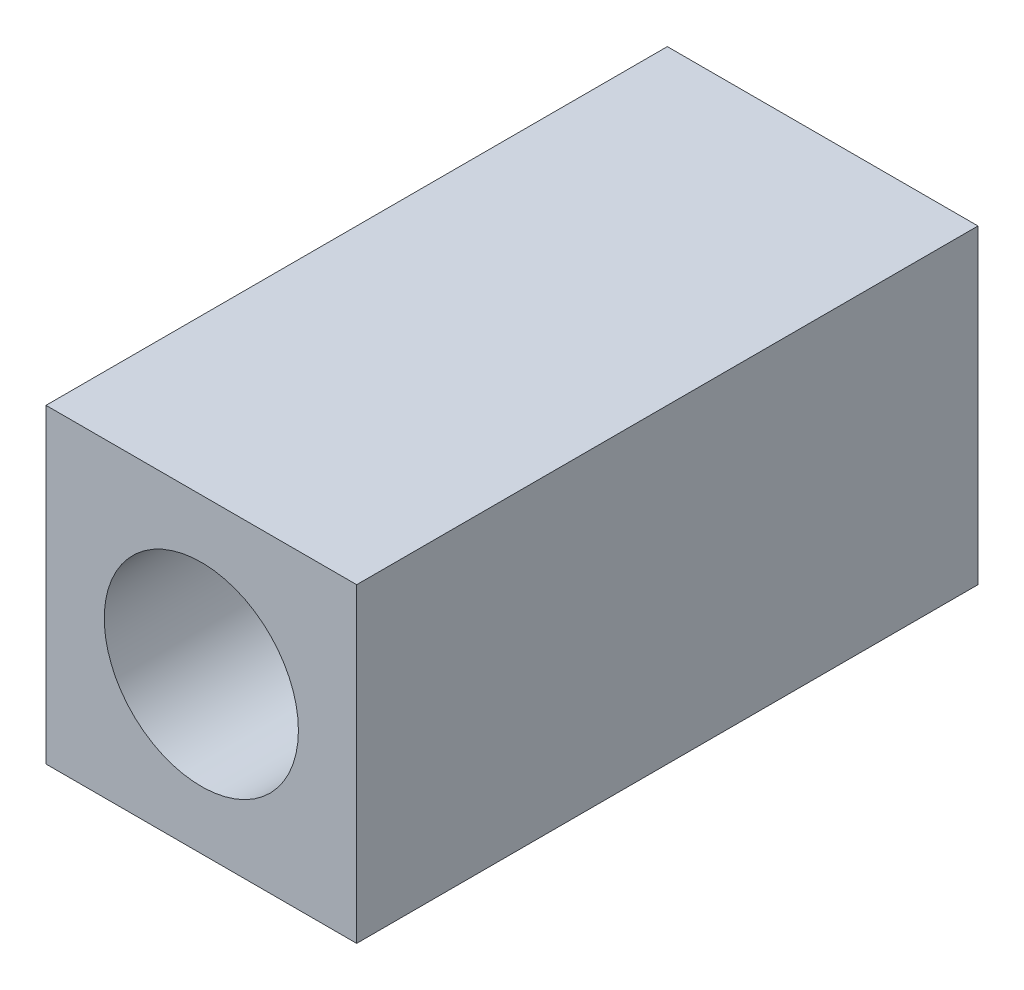
SolidWorks part; units mm, degrees
ref_plane "Front Plane" through (0, 0, 0) normal (0, 0, 1) x (1, 0, 0)
ref_plane "Top Plane" through (0, 0, 0) normal (0, 1, 0) x (1, 0, 0)
ref_plane "Right Plane" through (0, 0, 0) normal (1, 0, 0) x (0, 0, -1)
sketch "Sketch1" plane through (0, 0, 0) normal (0, 0, 1) x (1, 0, 0)
  line L0 (-6.35, -6.35) -> (6.35, -6.35)
  line L1 (6.35, -6.35) -> (6.35, 6.35)
  line L2 (6.35, 6.35) -> (-6.35, 6.35)
  line L3 (-6.35, 6.35) -> (-6.35, -6.35)
  point P4 (0, 6.35)
  point P6 (-6.35, 0)
  dimension "D1" = 12.7
extrude "Boss-Extrude1" add sketch "Sketch1" along normal blind 25.4
sketch "Sketch2" plane through (0, 0, 0) normal (0, 0, -1) x (-1, 0, 0)
  circle A0 centre (0, 0) radius 3.175
  dimension "D1" = 6.35
extrude "Cut-Extrude1" cut sketch "Sketch2" against normal blind 12.7
sketch "Sketch3" plane through (0, 0, 25.4) normal (0, 0, 1) x (1, 0, 0)
  circle A0 centre (0, 0) radius 3.9688
  dimension "D1" = 7.9375
extrude "Cut-Extrude2" cut sketch "Sketch3" against normal blind 12.7
